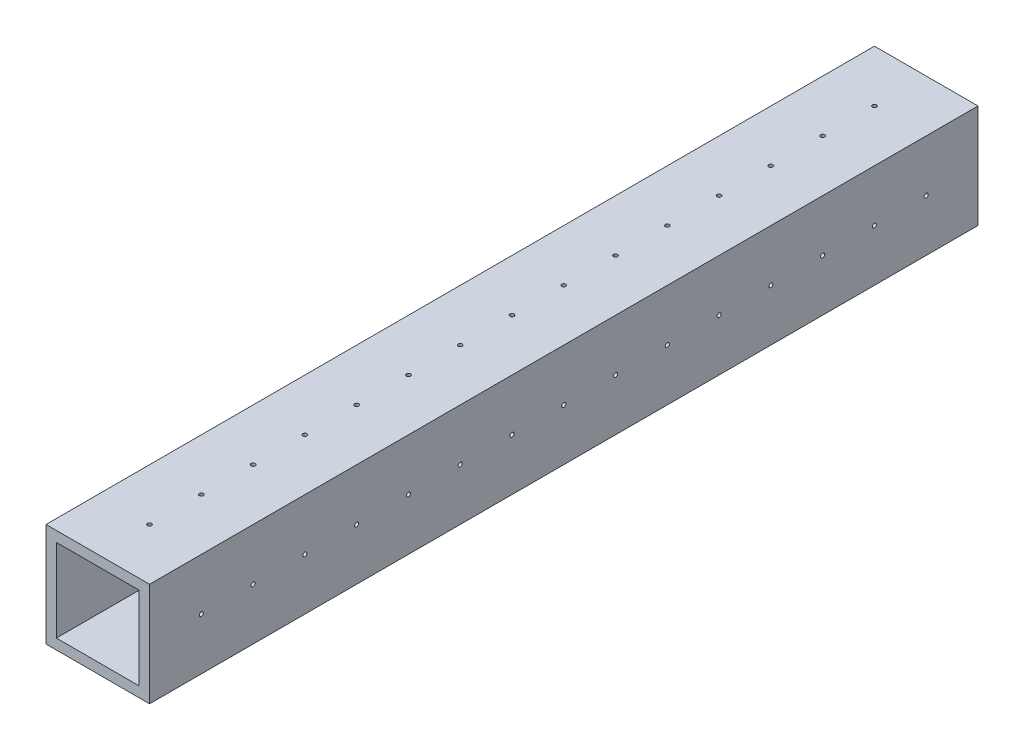
SolidWorks part; units mm, degrees
ref_plane "Front Plane" through (0, 0, 0) normal (0, 0, 1) x (1, 0, 0)
ref_plane "Top Plane" through (0, 0, 0) normal (0, 1, 0) x (1, 0, 0)
ref_plane "Right Plane" through (0, 0, 0) normal (1, 0, 0) x (0, 0, -1)
sketch "Sketch1" plane through (0, 0, 0) normal (0, 0, 1) x (1, 0, 0)
  line L1 (-4.0011, 9.8627) -> (16.3189, 9.8627)
  line L2 (-4.0011, 9.8627) -> (-4.0011, -10.4573)
  line L3 (-4.0011, -10.4573) -> (16.3189, -10.4573)
  line L4 (16.3189, 9.8627) -> (16.3189, -10.4573)
  line L5 (-6.5411, 12.4027) -> (18.8589, 12.4027)
  line L6 (-6.5411, 12.4027) -> (-6.5411, -12.9973)
  line L7 (-6.5411, -12.9973) -> (18.8589, -12.9973)
  line L8 (18.8589, 12.4027) -> (18.8589, -12.9973)
  dimension "D1" = 25.4
  dimension "D2" = 25.4
  dimension "D3" = 2.54
  dimension "D4" = 2.54
  dimension "D5" = 2.54
  dimension "D6" = 2.54
extrude "Boss-Extrude1" add sketch "Sketch1" along normal blind 203.2
sketch "Sketch2" plane through (18.8589, 0, 0) normal (1, 0, 0) x (0, 0, -1)
  line L0 (-203.2, -12.9973) -> (0, -12.9973) construction
  line L1 (-203.2, -12.9973) -> (-203.2, 12.4027) construction
  circle A0 centre (-190.5, -0.2973) radius 0.5
  circle A1 centre (-177.8, -0.2973) radius 0.5
  circle A2 centre (-165.1, -0.2973) radius 0.5
  circle A3 centre (-152.4, -0.2973) radius 0.5
  circle A4 centre (-139.7, -0.2973) radius 0.5
  circle A5 centre (-127, -0.2973) radius 0.5
  circle A6 centre (-114.3, -0.2973) radius 0.5
  circle A7 centre (-101.6, -0.2973) radius 0.5
  circle A8 centre (-88.9, -0.2973) radius 0.5
  circle A9 centre (-76.2, -0.2973) radius 0.5
  circle A10 centre (-63.5, -0.2973) radius 0.5
  circle A11 centre (-50.8, -0.2973) radius 0.5
  circle A12 centre (-38.1, -0.2973) radius 0.5
  circle A13 centre (-25.4, -0.2973) radius 0.5
  circle A14 centre (-12.7, -0.2973) radius 0.5
  dimension "D3" = 1
  dimension "D1" = 12.7
  dimension "D2" = 12.7
  dimension "D4" = 15
extrude "Cut-Extrude1" cut sketch "Sketch2" against normal through all both and the other way through all
sketch "Sketch3" plane through (0, 12.4027, 0) normal (0, 1, 0) x (1, 0, 0)
  line L0 (18.8589, -203.2) -> (18.8589, 0) construction
  line L1 (18.8589, -203.2) -> (-6.5411, -203.2) construction
  circle A0 centre (6.1589, -190.5) radius 0.5
  circle A1 centre (6.1589, -177.8) radius 0.5
  circle A2 centre (6.1589, -165.1) radius 0.5
  circle A3 centre (6.1589, -152.4) radius 0.5
  circle A4 centre (6.1589, -139.7) radius 0.5
  circle A5 centre (6.1589, -127) radius 0.5
  circle A6 centre (6.1589, -114.3) radius 0.5
  circle A7 centre (6.1589, -101.6) radius 0.5
  circle A8 centre (6.1589, -88.9) radius 0.5
  circle A9 centre (6.1589, -76.2) radius 0.5
  circle A10 centre (6.1589, -63.5) radius 0.5
  circle A11 centre (6.1589, -50.8) radius 0.5
  circle A12 centre (6.1589, -38.1) radius 0.5
  circle A13 centre (6.1589, -25.4) radius 0.5
  circle A14 centre (6.1589, -12.7) radius 0.5
  dimension "D1" = 12.7
  dimension "D3" = 1
  dimension "D2" = 12.7
  dimension "D4" = 15
extrude "Cut-Extrude2" cut sketch "Sketch3" against normal through all both and the other way through all
